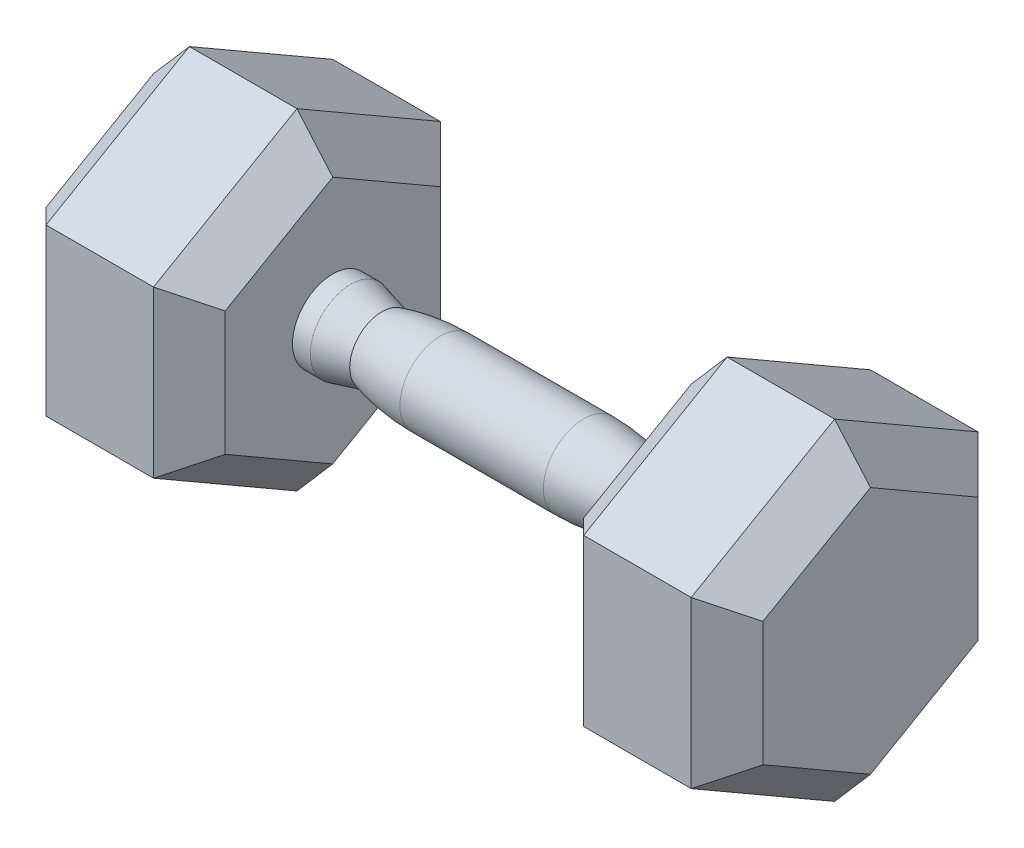
SolidWorks part; units mm, degrees
material "Plain Carbon Steel"
ref_plane "Front Plane" through (0, 0, 0) normal (1, 0, 0) x (0, 1, 0)
ref_plane "Top Plane" through (0, 0, 0) normal (0, 0, 1) x (0, 1, 0)
ref_plane "Right Plane" through (0, 0, 0) normal (0, 1, 0) x (-1, 0, 0)
sketch "Sketch1" plane through (0, 0, 0) normal (1, 0, 0) x (0, 1, 0)
  line L1 (58.6588, 0) -> (29.3294, 50.8)
  line L2 (29.3294, 50.8) -> (-29.3294, 50.8)
  line L3 (-29.3294, 50.8) -> (-58.6588, 0)
  line L4 (-58.6588, 0) -> (-29.3294, -50.8)
  line L5 (-29.3294, -50.8) -> (29.3294, -50.8)
  line L6 (29.3294, -50.8) -> (58.6588, 0)
  circle A0 centre (0, 0) radius 50.8 construction
  dimension "D1" = 101.6
extrude "Boss-Extrude1" add sketch "Sketch1" along normal blind 63.5
chamfer "Chamfer1" distance 12.7 angle 45 6 edges at (63.5, -43.9941, 25.4) (63.5, -43.9941, -25.4) (63.5, 0, -50.8) (63.5, 43.9941, -25.4) (63.5, 43.9941, 25.4) (63.5, 0, 50.8)
chamfer "Chamfer2" distance 12.7 angle 45 6 edges at (0, 43.9941, -25.4) (0, 0, -50.8) (0, -43.9941, -25.4) (0, -43.9941, 25.4) (0, 0, 50.8) (0, 43.9941, 25.4)
sketch "Sketch2" plane through (0, 0, 0) normal (0, 1, 0) x (-1, 0, 0)
  line L0 (0, 0) -> (0, 14.2875)
  line L1 (0, 38.1) -> (0, 0) construction
  line L2 (0, 14.2875) -> (6.35, 14.2875)
  line L3 (6.35, 14.2875) -> (17.4283, 11.43)
  line L5 (38.1, 14.2875) -> (63.5, 14.2875)
  line L6 (63.5, 14.2875) -> (63.5, 0)
  line L7 (63.5, 0) -> (0, 0)
  arc A0 (17.4283, 11.43) -> (38.1, 14.2875) centre (38.1, -61.9125) cw
  point P5 (28.5994, 14.2875)
  point P13 (16.1654, 11.43)
  dimension "D5" = 76.2
  dimension "D1" = 6.35
  dimension "D2" = 11.43
  dimension "D3" = 14.2875
  dimension "D4" = 63.5
  dimension "D6" = 25.4
revolve "Revolve1" add sketch "Sketch2" angle 360 about L7
mirror "Mirror1" about plane through (-63.5, 0, 14.2875) normal (-1, 0, 0) of bodies 102
